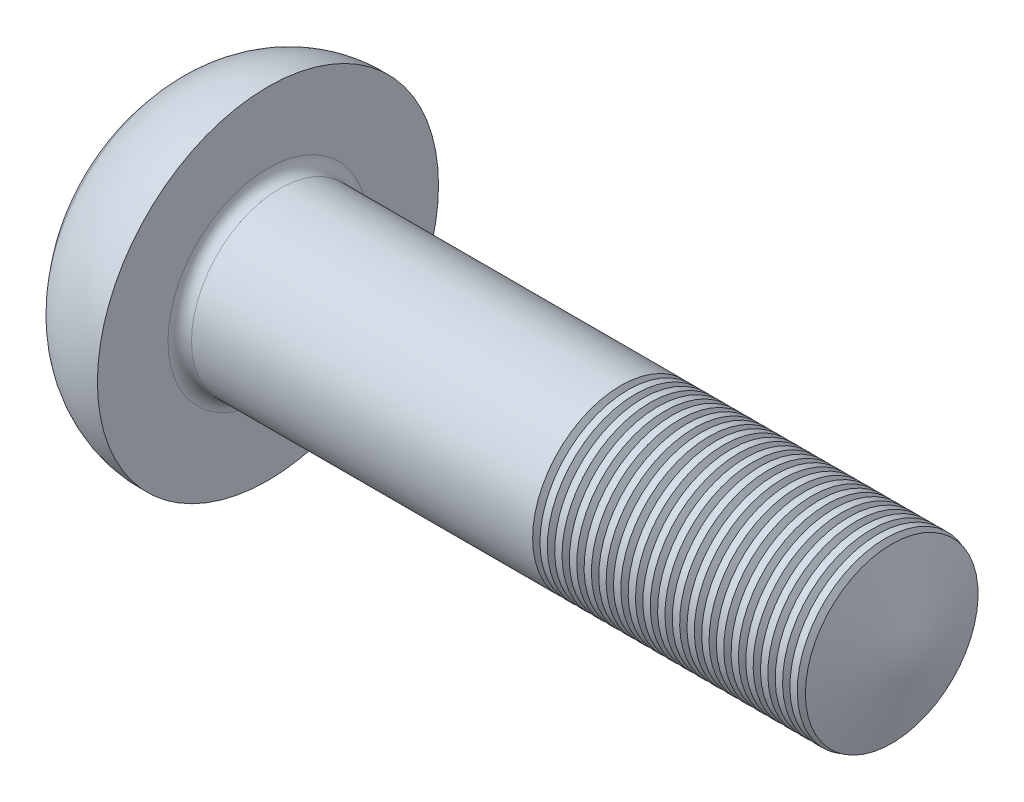
SolidWorks part; units mm, degrees
ref_plane "Front" through (0, 0, 0) normal (0, 0, 1) x (1, 0, 0)
ref_plane "Top" through (0, 0, 0) normal (0, 1, 0) x (1, 0, 0)
ref_plane "Right" through (0, 0, 0) normal (1, 0, 0) x (0, 0, -1)
sketch "Sketch1" plane through (0, 0, 0) normal (0, 1, 0) x (1, 0, 0)
  line L0 (-13.6293, 0) -> (11.3577, 0) construction
  line L1 (2.37, 1.5) -> (13.37, 1.5)
  line L2 (13.37, 1.5) -> (13.37, 0)
  line L3 (2.37, 1.5) -> (2.37, 2.9)
  line L4 (13.37, 0) -> (0, 0)
  arc A0 (2.37, 2.9) -> (0.8698, 2.2711) centre (2.2837, 1.002) ccw
  arc A1 (0, 0) -> (0.8698, 2.2711) centre (3.4, 0) cw
  dimension "r2" = 1.9
  dimension "r1" = 3.4
  dimension "d" = 3
  dimension "dk" = 5.8
  dimension "k" = 2.37
  dimension "l" = 11
revolve "Revolve1" add sketch "Sketch1" angle 360 about L0
cosmetic thread "ThreadCosmetic1" [suppressed] parameters "l0"=3.5, "dm"=2.75
fillet "Fillet2" radius 0.2 1 edges at (2.37, 0, 1.5)
sketch "Sketch4" plane through (0, 0, 0) normal (0, 1, 0) x (1, 0, 0)
  line L0 (4.7828, 0) -> (7.1391, 0) construction
  line L2 (14.1035, 0) -> (14.1035, 21)
  line L3 (14.1035, 21) -> (7.7431, 21)
  line L4 (7.7431, 21) -> (13.37, 0)
  line L5 (13.37, 0) -> (14.1035, 0)
  line L7 (13.37, -1.5) -> (13.37, 1.5) construction
  dimension "D1" = 75
  dimension "D2" = 0.7335
  dimension "D3" = 21
revolve "Cut-Revolve1" cut sketch "Sketch4" angle 360 about L0
sketch "Sketch2" plane through (0, 0, 0) normal (1, 0, 0) x (0, 0, -1)
  line L0 (-2.278, 0) -> (2.6944, 0) construction
  line L1 (0, -2.1234) -> (0, 2.1948) construction
  line L2 (-0.4625, 0.4625) -> (-1.85, 0.4625)
  line L3 (0.4625, -1.85) -> (-0.4625, -1.85)
  line L4 (0.4625, -1.85) -> (0.4625, -0.4625)
  line L5 (0.4625, 1.85) -> (-0.4625, 1.85)
  line L6 (-0.4625, -1.85) -> (-0.4625, -0.4625)
  line L7 (1.85, 0.4625) -> (0.4625, 0.4625)
  line L8 (1.85, 0.4625) -> (1.85, -0.4625)
  line L9 (1.85, -0.4625) -> (0.4625, -0.4625)
  line L10 (-1.85, 0.4625) -> (-1.85, -0.4625)
  line L11 (-0.4625, 0.4625) -> (-0.4625, 1.85)
  line L12 (-0.4625, -0.4625) -> (-1.85, -0.4625)
  line L13 (0.4625, 0.4625) -> (0.4625, 1.85)
  point P19 (-0.4625, 0.4625)
  point P22 (0.4625, 0.4625)
  point P27 (-0.4625, -0.4625)
  dimension "m" = 3.7
  dimension "D2" = 3.7
  dimension "D3" = 0.925
  dimension "D4" = 0.925
ref_plane "Plane1" through (2.62, 0, 0) normal (1, 0, 0) x (0, 0, -1)
sketch "Sketch5" plane through (2.62, 0, 0) normal (1, 0, 0) x (0, 0, -1)
  point P0 (0, 0)
loft "Cut-Loft1" cut profiles "Sketch5", "Sketch2"
sketch "Sketch6" plane through (0, 0, 0) normal (0, 0, 1) x (1, 0, 0)
  line L0 (8.37, 1.7) -> (8.495, 1.7)
  line L1 (8.495, 1.7) -> (8.495, 1.5)
  line L2 (8.495, 1.5) -> (8.4325, 1.3917)
  line L3 (8.37, 1.5) -> (8.4325, 1.3917)
  line L4 (8.37, 1.7) -> (8.37, 1.5)
  line L5 (10.7743, 0) -> (0, 0) construction
  line L6 (8.37, 1.5) -> (8.495, 1.5) construction
  line L7 (8.4325, 1.5) -> (8.4325, 1.3917) construction
  line L8 (12.9681, 1.5) -> (2.57, 1.5) construction
  point P5 (8.4325, 1.7)
  dimension "D1" = 0.2
  dimension "D2" = 0.125
  dimension "D3" = 5
revolve "Cut-Revolve10" cut sketch "Sketch6" angle 360 about L5
pattern_linear "LPattern10" count 20 spacing 0.25 along (1, 0, 0) of "Cut-Revolve10"
equation "\"D4@Sketch2\" = \"D3@Sketch2\""
equation "\"D2@Sketch2\" = \"m@Sketch2\""
equation "\"D3@Sketch2\" = \"m@Sketch2\" / 4"
equation "\"D2@Sketch6\" = (  \"d@Sketch1\" - \"dm@ThreadCosmetic1\" )  / 2"
equation "\"D3@Sketch6\" = \"l0@ThreadCosmetic1\" + \"d@Sketch1\" / 2"
equation "\"D3@LPattern10\" = \"D2@Sketch6\" *2"
equation "\"D1@LPattern10\" = \"D3@Sketch6\" / \"D3@LPattern10\""
